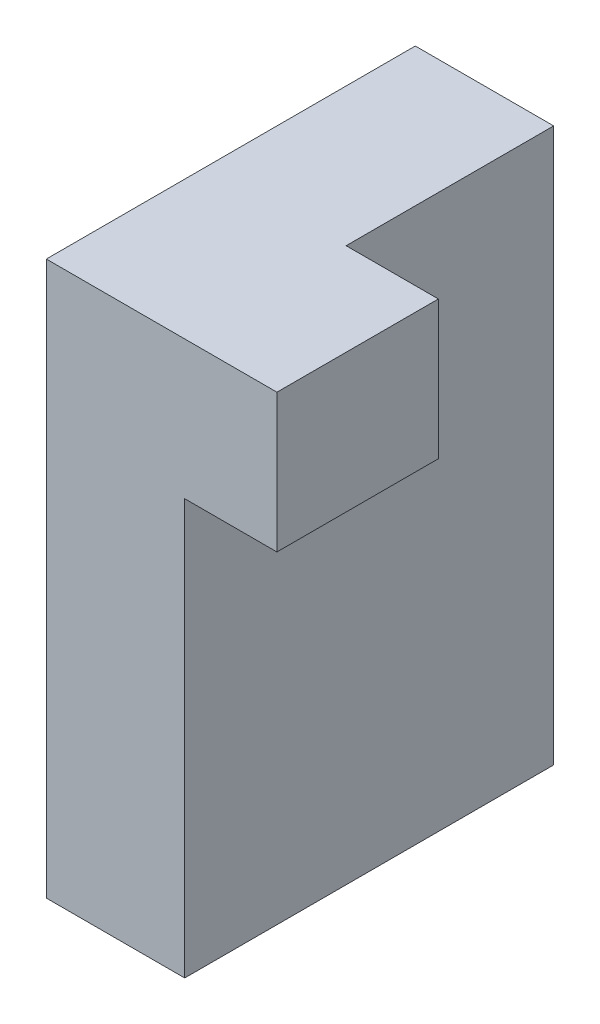
SolidWorks part; units mm, degrees
ref_plane "Front Plane" through (0, 0, 0) normal (0, 0, 1) x (1, 0, 0)
ref_plane "Top Plane" through (0, 0, 0) normal (0, 1, 0) x (1, 0, 0)
ref_plane "Right Plane" through (0, 0, 0) normal (1, 0, 0) x (0, 0, -1)
sketch "Sketch1" plane through (0, 0, 0) normal (1, 0, 0) x (0, 0, -1)
  line L1 (-25.4, 38.1) -> (25.4, 38.1)
  line L2 (-25.4, 38.1) -> (-25.4, -38.1)
  line L3 (-25.4, -38.1) -> (25.4, -38.1)
  line L4 (25.4, 38.1) -> (25.4, -38.1)
  dimension "D1" = 25.4
  dimension "D2" = 25.4
  dimension "D3" = 38.1
  dimension "D4" = 38.1
extrude "Boss-Extrude1" add sketch "Sketch1" along normal mid plane 19.05
sketch "Sketch3" plane through (9.525, 0, 0) normal (1, 0, 0) x (0, 0, -1)
  line L1 (-25.4, 38.1) -> (-3.175, 38.1)
  line L2 (-25.4, 38.1) -> (-25.4, 19.05)
  line L3 (-25.4, 19.05) -> (-3.175, 19.05)
  line L4 (-3.175, 38.1) -> (-3.175, 19.05)
  dimension "D1" = 3.175
  dimension "D2" = 19.05
extrude "Boss-Extrude3" add sketch "Sketch3" along normal blind 12.7
